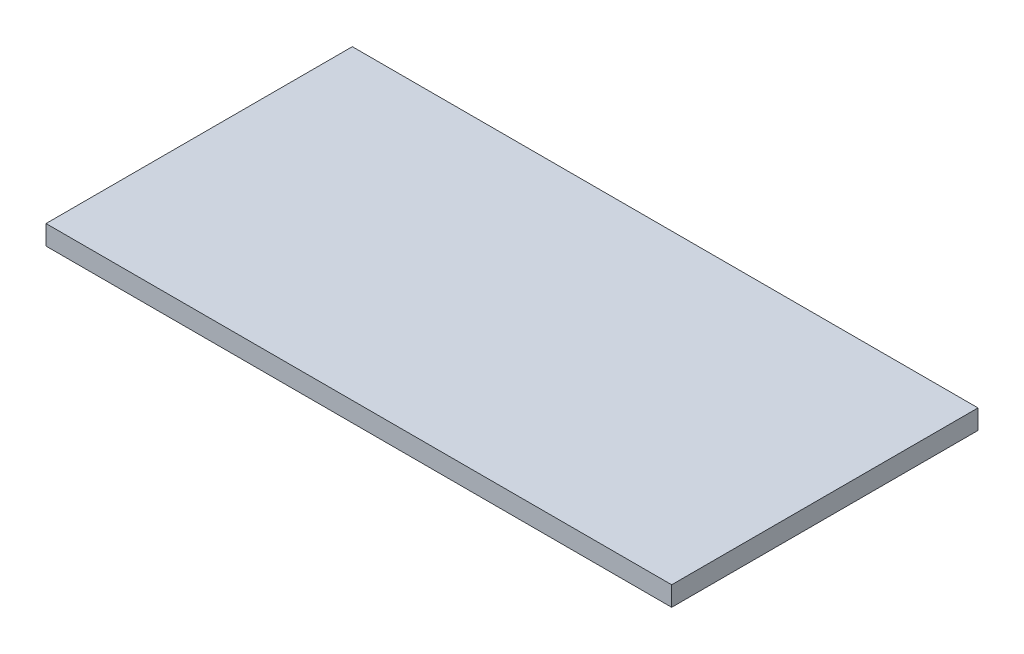
SolidWorks part; units mm, degrees
ref_plane "Спереди" through (0, 0, 0) normal (0, 0, 1) x (1, 0, 0)
ref_plane "Сверху" through (0, 0, 0) normal (0, 1, 0) x (1, 0, 0)
ref_plane "Справа" through (0, 0, 0) normal (1, 0, 0) x (0, 0, -1)
sketch "Эскиз1" plane through (0, 0, 0) normal (0, 1, 0) x (1, 0, 0)
  line L1 (288, -141) -> (-288, -141)
  line L2 (288, -141) -> (288, 141)
  line L3 (288, 141) -> (-288, 141)
  line L4 (-288, -141) -> (-288, 141)
  line L5 (288, -141) -> (-288, 141) construction
  line L6 (288, 141) -> (-288, -141) construction
  point P0 (0, 0)
  dimension "D1" = 576
  dimension "D2" = 282
extrude "Бобышка-Вытянуть1" add sketch "Эскиз1" along normal blind 18
